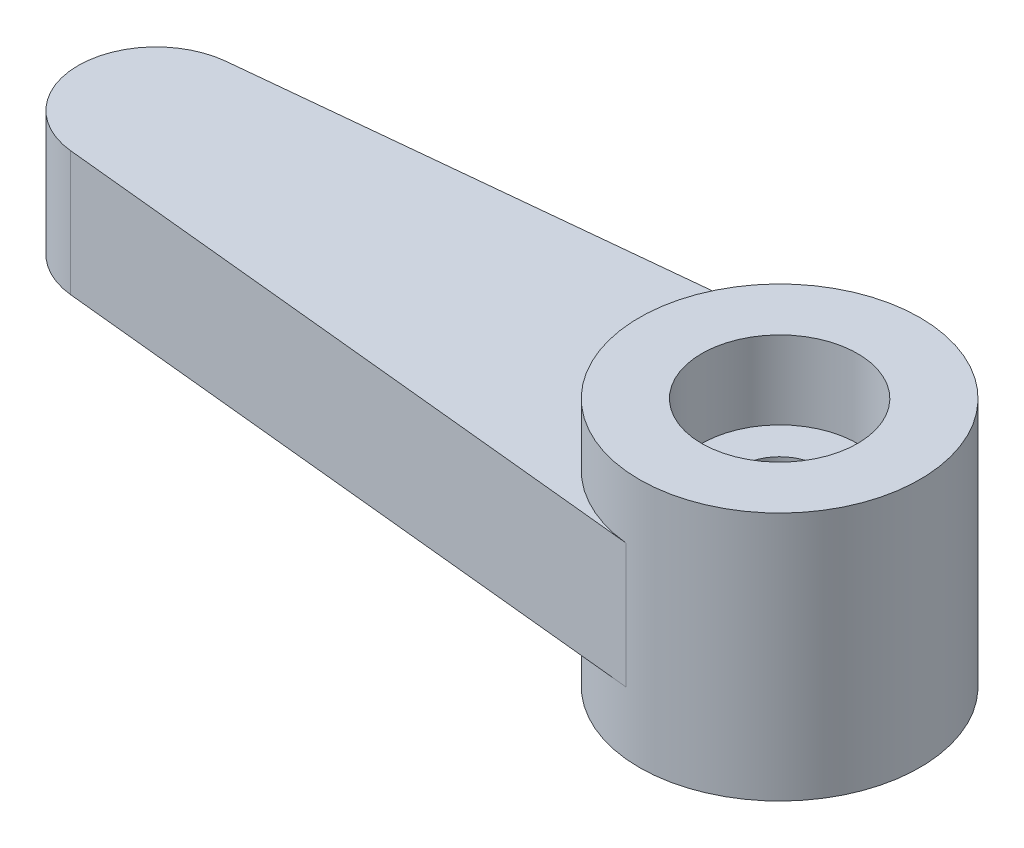
SolidWorks part; units mm, degrees
ref_plane "Alzado" through (0, 0, 0) normal (0, 0, 1) x (1, 0, 0)
ref_plane "Planta" through (0, 0, 0) normal (0, 1, 0) x (1, 0, 0)
ref_plane "Vista lateral" through (0, 0, 0) normal (1, 0, 0) x (0, 0, -1)
sketch "Croquis1" plane through (0, 0, 0) normal (1, 0, 0) x (0, 0, -1)
  line L0 (0, 9.0546) -> (0, 2.5821) construction
  line L1 (-4.5, 4) -> (-4.5, -4)
  line L2 (-4.5, -4) -> (-2.1589, -4)
  line L3 (-2.1589, -4) -> (-2.1589, -1.5)
  line L4 (-2.1589, -1.5) -> (-1.25, -1.5)
  line L6 (-1.25, 1.5) -> (-2.5, 1.5)
  line L7 (-2.5, 1.5) -> (-2.5, 4)
  line L8 (-2.5, 4) -> (-4.5, 4)
  line L9 (-1.25, 1.5) -> (-1.25, -1.5)
  line L10 (0, -1.9062) -> (0, -10.7072) construction
  dimension "D1" = 5
  dimension "D2" = 9
  dimension "D3" = 8
  dimension "D4" = 3
  dimension "D5" = 1.5
revolve "Revolución1" add sketch "Croquis1" angle 360 about L0
sketch "Croquis2" plane through (0, 0, 0) normal (0, 1, 0) x (1, 0, 0)
  line L0 (-20.25, 2.4875) -> (-0.45, 4.4774)
  line L1 (-0.45, -4.4774) -> (-20.25, -2.4875)
  arc A0 (-20.25, 2.4875) -> (-20.25, -2.4875) centre (-20, 0) ccw
  circle A1 centre (0, 0) radius 4.5 construction
  arc A2 (-0.45, 4.4774) -> (-0.45, -4.4774) centre (0, 0) ccw
  point P6 (0, 0)
  dimension "D1" = 5
  dimension "D2" = 20
extrude "Saliente-Extruir1" add sketch "Croquis2" along normal blind 2 and the other way blind 2
